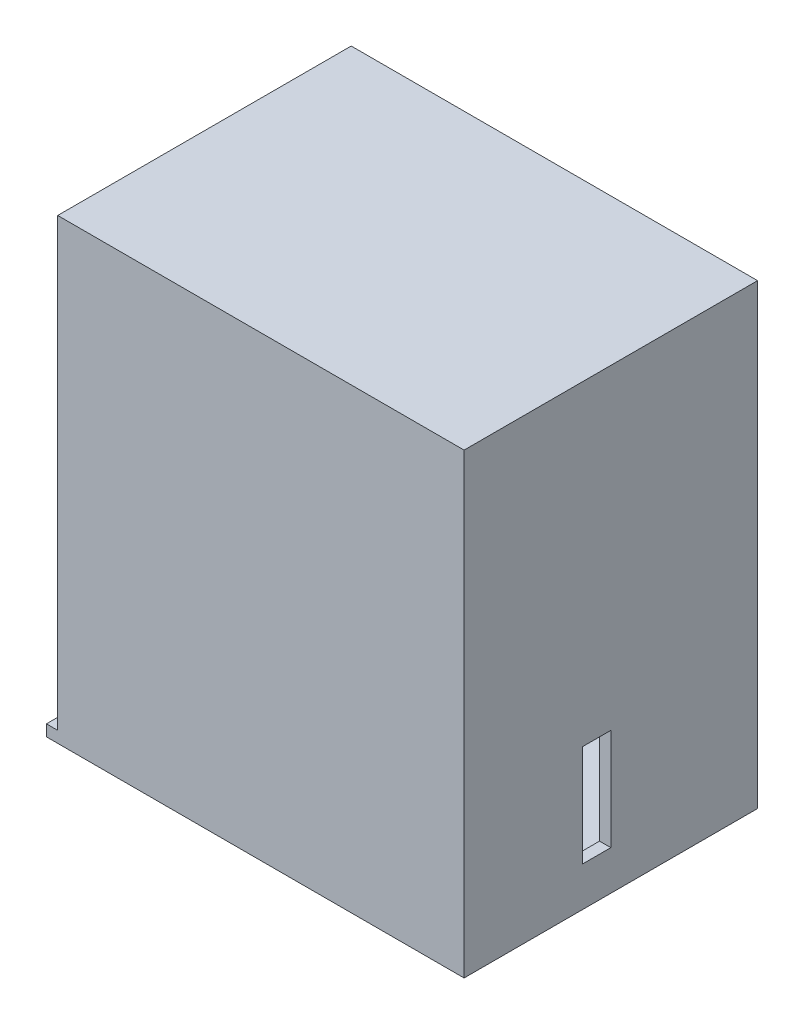
SolidWorks part; units mm, degrees
ref_plane "Ebene vorne" through (0, 0, 0) normal (0, 0, 1) x (1, 0, 0)
ref_plane "Ebene oben" through (0, 0, 0) normal (0, 1, 0) x (1, 0, 0)
ref_plane "Ebene rechts" through (0, 0, 0) normal (1, 0, 0) x (0, 0, -1)
sketch "Skizze1" plane through (0, 0, 0) normal (0, 0, 1) x (1, 0, 0)
  line L1 (-9.4467, 4.2096) -> (-79.4467, 4.2096)
  line L2 (-9.4467, 4.2096) -> (-9.4467, -72.7904)
  line L3 (-9.4467, -72.7904) -> (-79.4467, -72.7904)
  line L4 (-79.4467, 4.2096) -> (-79.4467, -72.7904)
  dimension "D1" = 70
  dimension "D2" = 77
extrude "Aufsatz-Linear austragen1" add sketch "Skizze1" along normal blind 2
sketch "Skizze2" plane through (-9.4467, 0, 0) normal (1, 0, 0) x (0, 0, -1)
  line L0 (24, -67.7904) -> (19, -67.7904) construction
  line L1 (-2, 4.2096) -> (50, 4.2096)
  line L2 (-2, 4.2096) -> (-2, -72.7904)
  line L3 (-2, -72.7904) -> (50, -72.7904)
  line L4 (50, 4.2096) -> (50, -72.7904)
  line L5 (24, -49.7904) -> (19, -49.7904) construction
  line L6 (19, -67.7904) -> (19, -49.7904) construction
  line L7 (24, -67.7904) -> (24, -49.7904) construction
  line L8 (24, -67.7904) -> (19, -67.7904)
  line L9 (24, -49.7904) -> (19, -49.7904)
  line L10 (19, -67.7904) -> (19, -49.7904)
  line L11 (24, -67.7904) -> (24, -49.7904)
  dimension "D1" = 52
extrude "Aufsatz-Linear austragen2" add sketch "Skizze2" along normal blind 2
sketch "Skizze3" plane through (0, -72.7904, 0) normal (0, -1, 0) x (1, 0, 0)
  line L1 (-7.4467, -50) -> (-81.4467, -50)
  line L2 (-7.4467, -50) -> (-7.4467, 2)
  line L3 (-7.4467, 2) -> (-81.4467, 2)
  line L4 (-81.4467, -50) -> (-81.4467, 2)
  line L5 (-45.3978, -35) -> (-73.3978, -35)
  line L6 (-45.3978, -35) -> (-45.3978, -29)
  line L7 (-45.3978, -32) -> (-45.3978, -19) construction
  line L8 (-45.3978, -29) -> (-73.3978, -29)
  line L9 (-73.3978, -32) -> (-73.3978, -19) construction
  line L10 (-73.3978, -29) -> (-73.3978, -35)
  dimension "D1" = 74
  dimension "D2" = 6
  dimension "D3" = 15
extrude "Aufsatz-Linear austragen3" add sketch "Skizze3" along normal blind 2
sketch "Skizze9" plane through (0, 4.2096, 0) normal (0, 1, 0) x (1, 0, 0)
  line L1 (-79.4467, -2) -> (-7.4467, -2)
  line L2 (-79.4467, -2) -> (-79.4467, 50)
  line L3 (-79.4467, 50) -> (-7.4467, 50)
  line L4 (-7.4467, -2) -> (-7.4467, 50)
extrude "Aufsatz-Linear austragen7" add sketch "Skizze9" along normal blind 2
